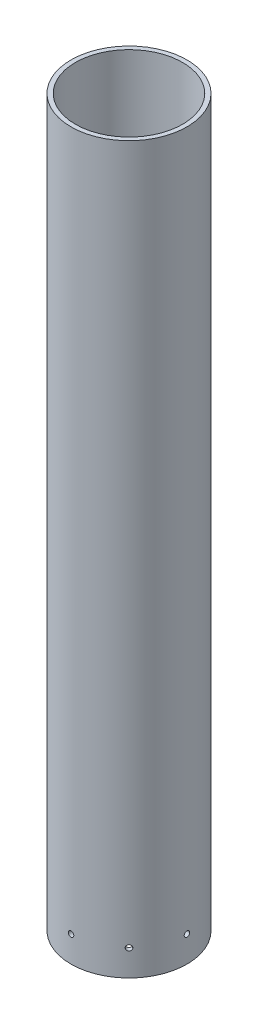
SolidWorks part; units mm, degrees
material "Acrylic (Medium-high impact)"
ref_plane "Front Plane" through (0, 0, 0) normal (0, 0, 1) x (1, 0, 0)
ref_plane "Top Plane" through (0, 0, 0) normal (0, 1, 0) x (1, 0, 0)
ref_plane "Right Plane" through (0, 0, 0) normal (1, 0, 0) x (0, 0, -1)
sketch "Sketch1" plane through (0, 0, 0) normal (0, 1, 0) x (1, 0, 0)
  circle A0 centre (0, 0) radius 40
  circle A1 centre (0, 0) radius 36.95
  dimension "D1" = 73.9
  dimension "D2" = 80
extrude "Boss-Extrude1" add sketch "Sketch1" along normal blind 500
sketch "Sketch2" plane through (0, 0, 0) normal (0, 0, 1) x (1, 0, 0)
  line L1 (0, 18) -> (-12.0277, 18)
  line L4 (0, 0) -> (0, 35)
  circle A0 centre (0, 18) radius 1.9
  point P10 (0, 26)
  point P11 (0, 18)
  dimension "D4" = 35
  dimension "D1" = 3.8
  dimension "D5" = 9
  dimension "D6" = 8
extrude "Cut-Extrude1" cut sketch "Sketch2" against normal blind 66
pattern_circular "CirPattern2" count 8 every 45 about axis through (0, 500, 0) along (0, -1, 0) of "Cut-Extrude1"
ref_plane "Plane1" through (0, 18, 0) normal (0, -1, 0) x (-1, 0, 0)
split line "Split Line4"
